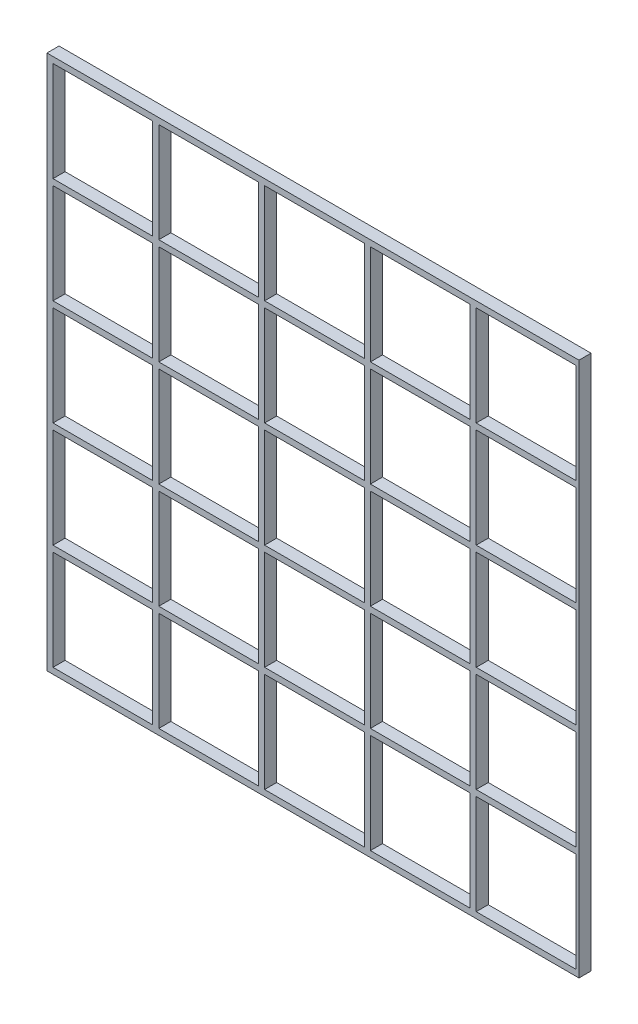
SolidWorks part; units mm, degrees
ref_plane "Alzado" through (0, 0, 0) normal (0, 0, 1) x (1, 0, 0)
ref_plane "Planta" through (0, 0, 0) normal (0, 1, 0) x (1, 0, 0)
ref_plane "Vista lateral" through (0, 0, 0) normal (1, 0, 0) x (0, 0, -1)
sketch "Croquis1" plane through (0, 0, 0) normal (0, 0, 1) x (1, 0, 0)
  line L5 (36, 1) -> (36, -1)
  line L6 (34, -1) -> (1, -1)
  line L7 (34, -1) -> (34, -34)
  line L8 (36, 1) -> (36, -36)
  line L10 (36, -36) -> (-1, -36)
  line L11 (-1, -36) -> (-1, 1)
  line L12 (-1, 1) -> (36, 1)
  line L13 (1, -1) -> (1, -34)
  line L14 (1, -34) -> (34, -34)
extrude "Saliente-Extruir1" add sketch "Croquis1" along normal blind 4 contours L8 L10 L11 L12 | L13 L14 L7 L6
pattern_linear "MatrizL1" count 5 spacing 35 along (-1, 0, 0) count 5 spacing 35 along (0, 1, 0) of "Saliente-Extruir1"
sketch "Croquis2" plane through (0, 0, 4) normal (0, 0, 1) x (1, 0, 0)
  line L0 (36, -36) -> (-141, -36) construction
  line L1 (36, 141) -> (35, 141)
  line L2 (36, 141) -> (36, -36)
  line L3 (36, -36) -> (35, -36)
  line L4 (35, 141) -> (35, -36)
  dimension "D1" = 1
extrude "Cortar-Extruir1" cut sketch "Croquis2" against normal blind 10
